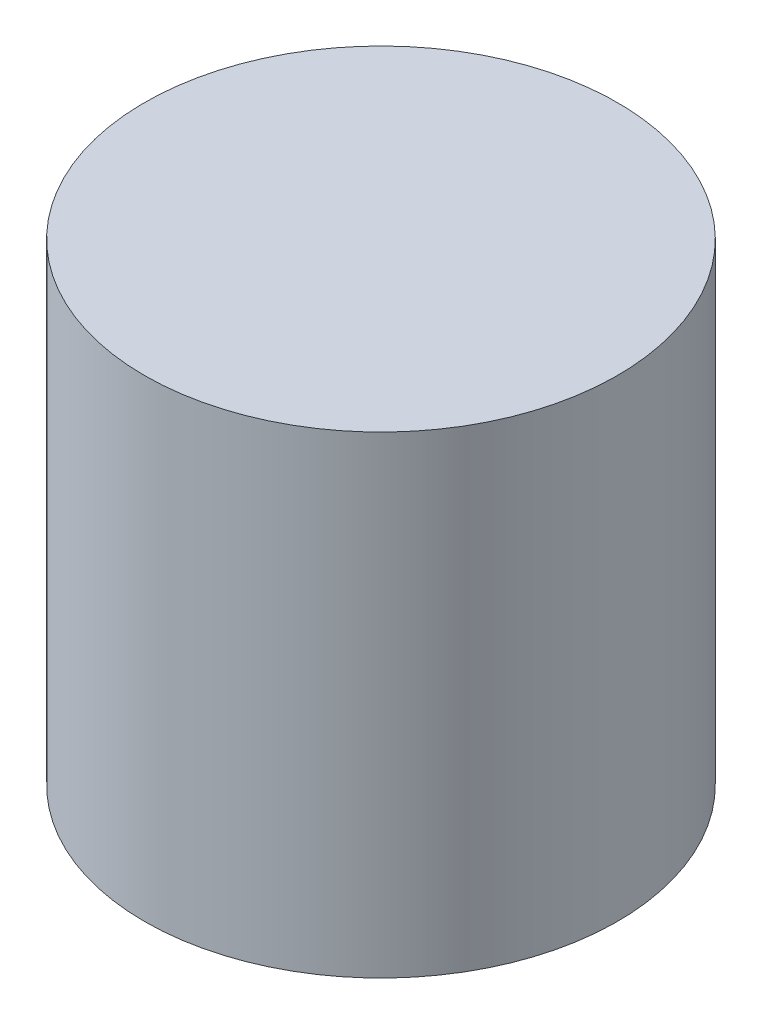
SolidWorks part; units mm, degrees
ref_plane "Front Plane" through (0, 0, 0) normal (0, 0, 1) x (1, 0, 0)
ref_plane "Top Plane" through (0, 0, 0) normal (0, 1, 0) x (1, 0, 0)
ref_plane "Right Plane" through (0, 0, 0) normal (1, 0, 0) x (0, 0, -1)
sketch "Sketch1" plane through (0, 0, 0) normal (0, 1, 0) x (1, 0, 0)
  circle A0 centre (-53.7316, 16.2522) radius 63.5
  dimension "D1" = 127
extrude "Boss-Extrude1" add sketch "Sketch1" along normal blind 127
